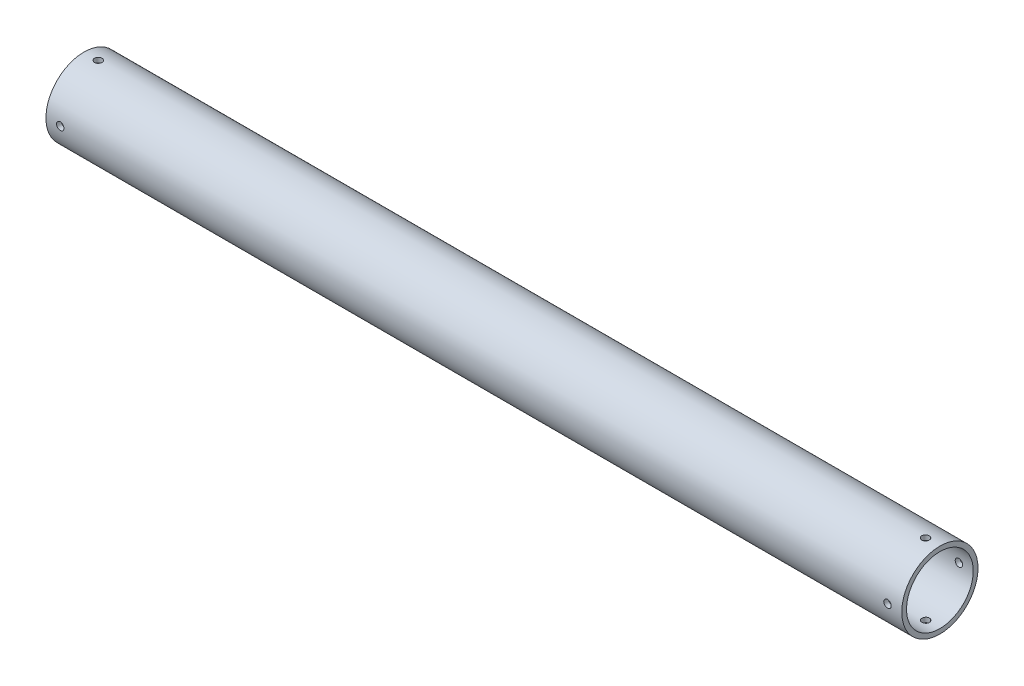
SolidWorks part; units mm, degrees
material "PC High Viscosity"
ref_plane "Front Plane" through (0, 0, 0) normal (0, 0, 1) x (1, 0, 0)
ref_plane "Top Plane" through (0, 0, 0) normal (0, 1, 0) x (1, 0, 0)
ref_plane "Right Plane" through (0, 0, 0) normal (1, 0, 0) x (0, 0, -1)
sketch "Sketch1" plane through (0, 0, 0) normal (1, 0, 0) x (0, 0, -1)
  circle A0 centre (0, 0) radius 25.4
  circle A1 centre (0, 0) radius 22.225
  dimension "D1" = 50.8
  dimension "D2" = 3.175
extrude "Boss-Extrude1" add sketch "Sketch1" along normal mid plane 570.23
sketch "Sketch2" plane through (0, 0, 0) normal (0, 0, 1) x (1, 0, 0)
  line L0 (-285.115, 25.4) -> (-285.115, -25.4) construction
  line L1 (285.115, -25.4) -> (285.115, 25.4) construction
  circle A0 centre (-275.59, 0) radius 2.4892
  circle A1 centre (275.59, 0) radius 2.4892
  dimension "D1" = 4.9784
  dimension "D2" = 9.525
  dimension "D3" = 9.525
extrude "Cut-Extrude1" cut sketch "Sketch2" against normal through all both and the other way through all
sketch "Sketch3" plane through (0, 0, 0) normal (0, 1, 0) x (1, 0, 0)
  line L3 (285.115, -22.225) -> (285.115, 22.225) construction
  line L4 (-285.115, 25.4) -> (-285.115, -25.4) construction
  circle A0 centre (-275.59, 0) radius 2.4892
  circle A1 centre (275.59, 0) radius 2.4892
  dimension "D1" = 4.9784
  dimension "D2" = 9.525
  dimension "D3" = 9.525
extrude "Cut-Extrude2" cut sketch "Sketch3" against normal through all both and the other way through all
